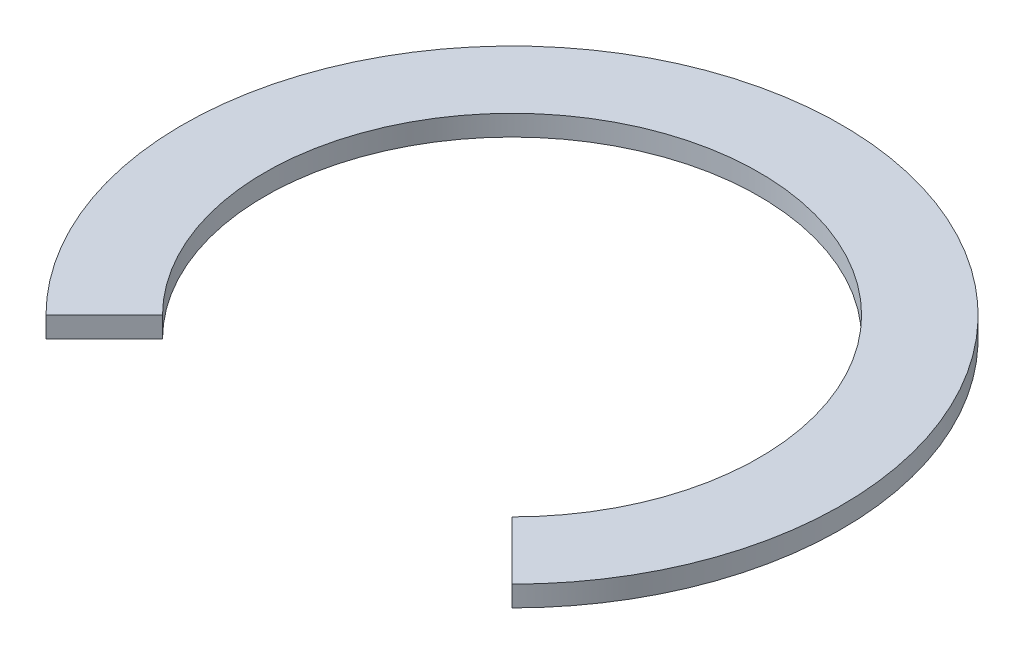
SolidWorks part; units mm, degrees
ref_plane "Front Plane" through (0, 0, 0) normal (0, 0, 1) x (1, 0, 0)
ref_plane "Top Plane" through (0, 0, 0) normal (0, 1, 0) x (1, 0, 0)
ref_plane "Right Plane" through (0, 0, 0) normal (1, 0, 0) x (0, 0, -1)
sketch "Sketch2" plane through (0, 0, 0) normal (0, 1, 0) x (1, 0, 0)
  circle A0 centre (0, 0) radius 12.7
  dimension "D1" = 25.4
extrude "Boss-Extrude1" add sketch "Sketch2" along normal blind 0.7937
sketch "Sketch3" plane through (0, 0.7937, 0) normal (0, 1, 0) x (1, 0, 0)
  circle A0 centre (0, 0) radius 9.525
extrude "Cut-Extrude1" cut sketch "Sketch3" against normal through all
sketch "Sketch4" plane through (0, 0, 0) normal (1, 0, 0) x (0, 0, -1)
  line L1 (0, -0.92) -> (-22.3182, -0.92)
  line L2 (0, -0.92) -> (0, 7.4371)
  line L3 (0, 7.4371) -> (-22.3182, 7.4371)
  line L4 (-22.3182, -0.92) -> (-22.3182, 7.4371)
revolve "Cut-Revolve1" cut sketch "Sketch4" angle 45 about L2 other way angle 45
